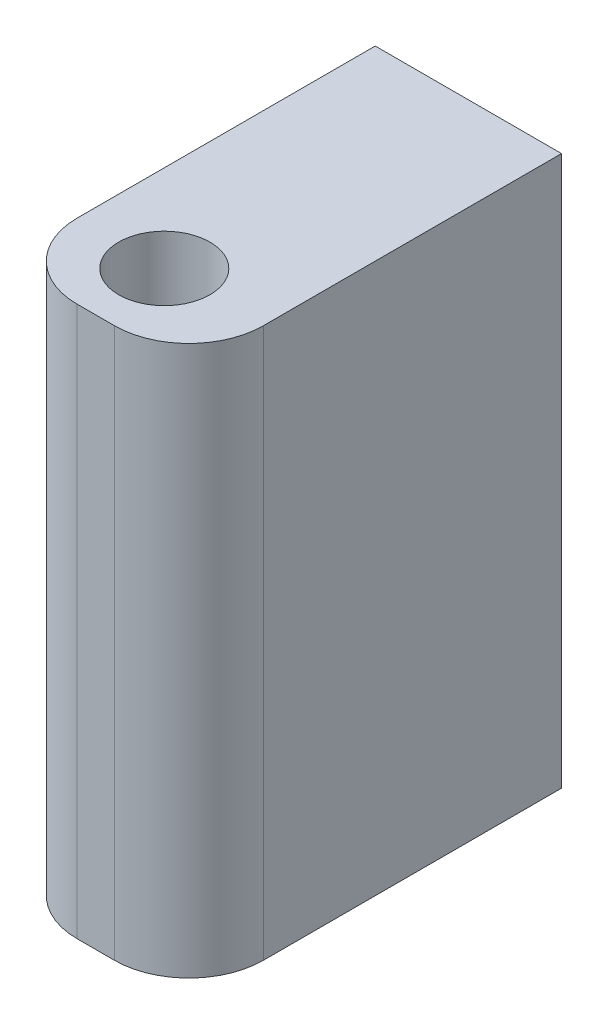
SolidWorks part; units mm, degrees
ref_plane "Front Plane" through (0, 0, 0) normal (0, 0, 1) x (1, 0, 0)
ref_plane "Top Plane" through (0, 0, 0) normal (0, 1, 0) x (1, 0, 0)
ref_plane "Right Plane" through (0, 0, 0) normal (1, 0, 0) x (0, 0, -1)
sketch "Sketch1" plane through (0, 0, 0) normal (0, 0, 1) x (1, 0, 0)
  line L1 (-4.678, 15.9148) -> (5.322, 15.9148)
  line L2 (-4.678, 15.9148) -> (-4.678, -13.5852)
  line L3 (-4.678, -13.5852) -> (5.322, -13.5852)
  line L4 (5.322, 15.9148) -> (5.322, -13.5852)
  dimension "D1" = 29.5
  dimension "D2" = 10
extrude "Extrude1" add sketch "Sketch1" along normal blind 20
sketch "Sketch2" plane through (0, 15.9148, 0) normal (0, 1, 0) x (-1, 0, 0)
  line L0 (-5.322, 20) -> (4.678, 20) construction
  circle A0 centre (0, 16) radius 2.45
  dimension "D1" = 4.9
  dimension "D2" = 4
extrude "Extrude2" cut sketch "Sketch2" against normal through all
sketch "Sketch4" plane through (0, 0, 0) normal (0, 0, 1) x (1, 0, 0)
  line L0 (5.322, 15.9148) -> (-4.678, 15.9148) construction
  circle A0 centre (0, 7.9148) radius 1.95
  circle A1 centre (0, -7.0852) radius 1.95
  dimension "D1" = 3.9
  dimension "D2" = 3.9
  dimension "D3" = 15
  dimension "D4" = 8
extrude "Extrude3" cut sketch "Sketch4" along normal blind 11
fillet "Fillet1" radius 4 2 edges at (-4.678, 1.1648, 20) (5.322, 1.1648, 20)
